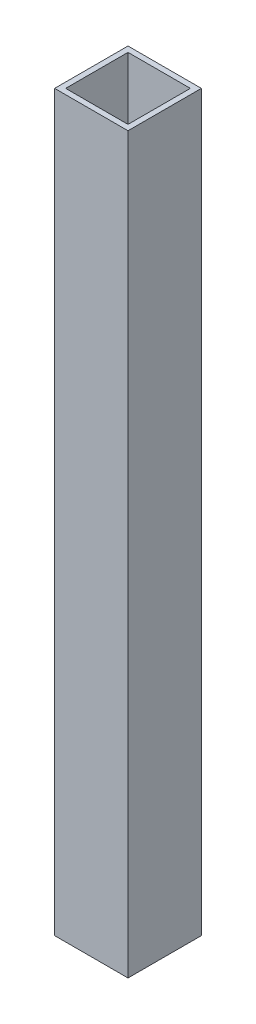
SolidWorks part; units mm, degrees
ref_plane "Front Plane" through (0, 0, 0) normal (0, 0, 1) x (1, 0, 0)
ref_plane "Top Plane" through (0, 0, 0) normal (0, 1, 0) x (1, 0, 0)
ref_plane "Right Plane" through (0, 0, 0) normal (1, 0, 0) x (0, 0, -1)
sketch "Sketch2" plane through (0, 0, 0) normal (0, 1, 0) x (1, 0, 0)
  line L1 (20, -20) -> (-20, -20)
  line L2 (20, -20) -> (20, 20)
  line L3 (20, 20) -> (-20, 20)
  line L4 (-20, -20) -> (-20, 20)
  line L5 (20, -20) -> (-20, 20) construction
  line L6 (20, 20) -> (-20, -20) construction
  point P0 (0, 0)
  dimension "D1" = 40
  dimension "D2" = 40
extrude "Boss-Extrude2" add sketch "Sketch2" along normal blind 400
sketch "Sketch3" plane through (0, 400, 0) normal (0, 1, 0) x (1, 0, 0)
  line L17 (17, -17) -> (17, 17)
  line L18 (-17, -17) -> (17, -17)
  line L19 (-17, 17) -> (-17, -17)
  line L20 (17, 17) -> (-17, 17)
  line L21 (17, -17) -> (17, 17)
  line L22 (-17, -17) -> (17, -17)
  line L23 (-17, 17) -> (-17, -17)
  line L24 (17, 17) -> (-17, 17)
  dimension "D1" = 3
extrude "Cut-Extrude1" cut sketch "Sketch3" against normal through all
